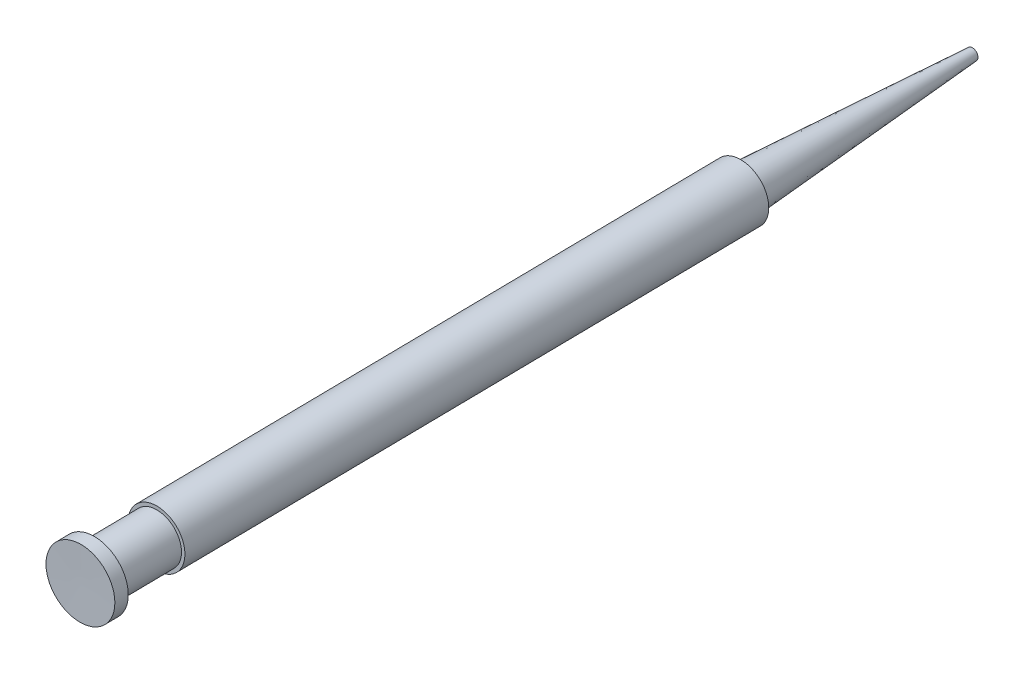
SolidWorks part; units mm, degrees
ref_plane "Front Plane" through (0, 0, 0) normal (0, 0, 1) x (1, 0, 0)
ref_plane "Top Plane" through (0, 0, 0) normal (0, 1, 0) x (1, 0, 0)
ref_plane "Right Plane" through (0, 0, 0) normal (1, 0, 0) x (0, 0, -1)
sketch "linear trace" plane through (0, 0, 0) normal (0, 1, 0) x (1, 0, 0)
  line L0 (160, 640) -> (800, 640) construction
  line L1 (24.5186, 43.7784) -> (24.8828, 17.0057)
  line L2 (24.8828, 17.0057) -> (25.8757, -55.9875)
  line L3 (25.1593, 43.7784) -> (27.244, 18.0728) construction
  line L4 (23.9729, 43.7784) -> (22.4925, 18.0728) construction
  line L5 (22.4925, 18.0728) -> (27.244, 18.0728) construction
  arc A0 (24.9673, 68.7253) -> (22.5853, 64.4044) centre (26.3322, 65.1559) ccw
  arc A1 (22.5853, 64.4044) -> (24.5186, 43.7784) centre (-74.8005, 44.8729) cw
  point P13 (24.8682, 18.0728)
sketch "Sketch2" plane through (0, 0, 0) normal (0, 1, 0) x (1, 0, 0)
  line L0 (24.8828, 17.0057) -> (25.8757, -55.9875) construction
  line L1 (24.5186, 43.7784) -> (24.8828, 17.0057) construction
  line L2 (24.8828, 17.0057) -> (25.8757, -55.9875)
  line L3 (24.5186, 43.7784) -> (24.8828, 17.0057)
  line L4 (24.5186, 43.7784) -> (25.1344, 43.7784)
  line L5 (25.1344, 43.7784) -> (27.1636, 17.8476)
  line L6 (27.9716, 17.8476) -> (28.8604, -47.4883)
  line L7 (28.4853, -47.4883) -> (28.5805, -54.4877)
  line L8 (28.5805, -54.4877) -> (29.6056, -54.4877)
  line L9 (29.6056, -54.4877) -> (29.626, -55.9875)
  line L10 (29.626, -55.9875) -> (25.8757, -55.9875)
  line L11 (28.4853, -47.4883) -> (28.8604, -47.4883)
  line L12 (27.1636, 17.8476) -> (27.9716, 17.8476)
  dimension "D1" = 3.1
  dimension "D2" = 73
  dimension "D3" = 2.725
  dimension "D4" = 3.75
  dimension "D5" = 1.5
  dimension "D6" = 7
revolve "Revolve4" add sketch "Sketch2" angle 360 about L2
